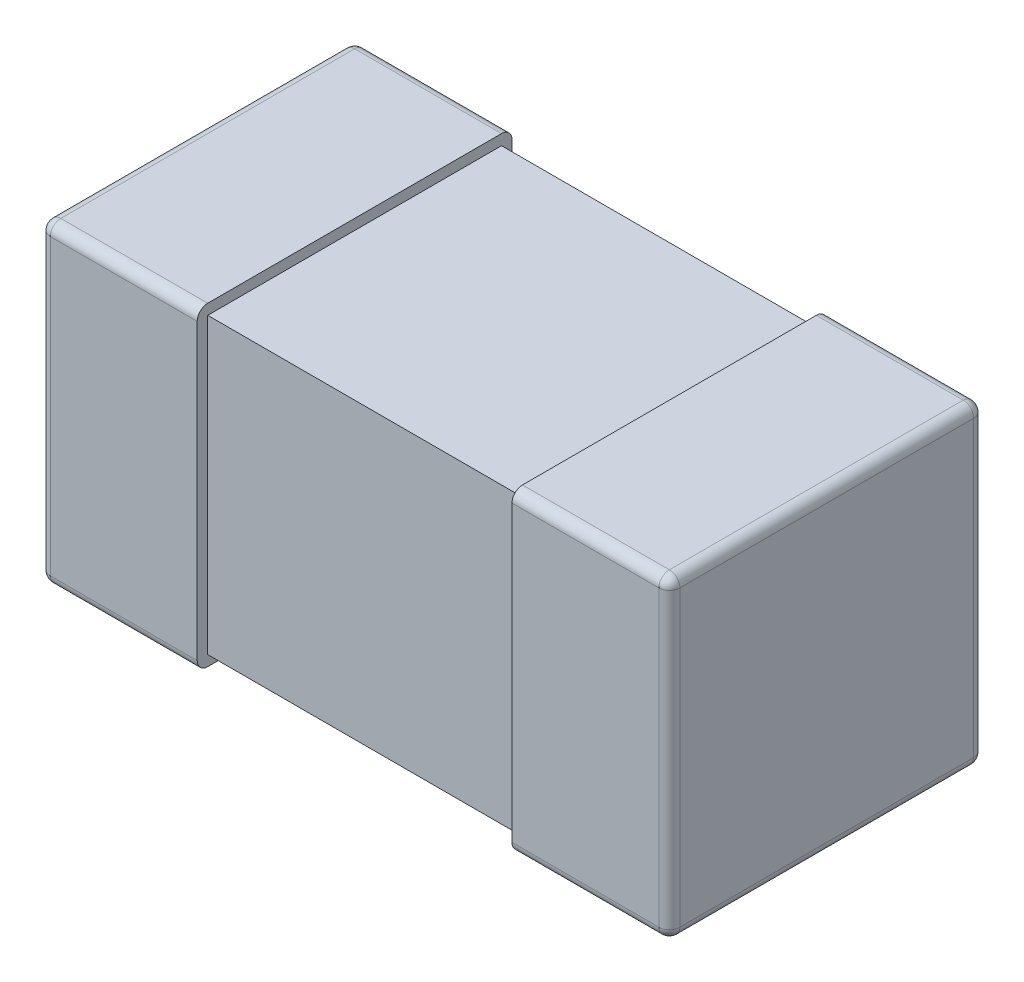
SolidWorks part; units mm, degrees
ref_plane "Front Plane" through (0, 0, 0) normal (0, 0, 1) x (1, 0, 0)
ref_plane "Top Plane" through (0, 0, 0) normal (0, 1, 0) x (1, 0, 0)
ref_plane "Right Plane" through (0, 0, 0) normal (1, 0, 0) x (0, 0, -1)
sketch "Sketch1" plane through (0, 0, 0) normal (0, 1, 0) x (1, 0, 0)
  line L0 (0, 0.15) -> (0, -0.15) construction
  line L1 (-0.3, 0) -> (0, 0) construction
  line L3 (-0.3, 0.15) -> (-0.15, 0.15)
  line L4 (-0.3, 0.15) -> (-0.3, -0.15)
  line L5 (-0.3, -0.15) -> (-0.15, -0.15)
  line L6 (-0.15, 0.15) -> (-0.15, -0.15)
  dimension "BANDWIDTH" = 0.15
  dimension "WIDTH" = 0.3
  dimension "LENGTH-HALF" = 0.3
extrude "THICKNESS" add sketch "Sketch1" along normal mid plane 0.3
fillet "Fillet1" radius 0.01 8 edges at (-0.3, -0.15, 0) (-0.225, -0.15, -0.15) (-0.3, 0, -0.15) (-0.225, -0.15, 0.15) (-0.3, 0, 0.15) (-0.3, 0.15, 0) (-0.225, 0.15, -0.15) (-0.225, 0.15, 0.15)
sketch "Sketch2" plane through (0, 0, 0) normal (1, 0, 0) x (0, 0, -1)
  line L0 (0, 0.15) -> (0, -0.15) construction
  line L1 (-0.14, 0.14) -> (0.14, 0.14)
  line L2 (-0.14, 0.14) -> (-0.14, -0.14)
  line L3 (-0.14, -0.14) -> (0.14, -0.14)
  line L4 (0.14, 0.14) -> (0.14, -0.14)
  line L5 (-0.14, 0.15) -> (0.14, 0.15) construction
  line L6 (-0.14, -0.15) -> (0.14, -0.15) construction
  line L7 (-0.15, 0) -> (0.15, 0) construction
  line L8 (-0.15, 0.14) -> (-0.15, -0.14) construction
  line L9 (0.15, 0.14) -> (0.15, -0.14) construction
  dimension "D1" = 0.01
  dimension "D2" = 0.01
extrude "Boss-Extrude2" add sketch "Sketch2" against normal up to surface (0.15 mm away) up to face at (-0.15, 0, 0)
mirror "Mirror3" about plane through (0, 0, 0) normal (1, 0, 0) of "Boss-Extrude2", "Fillet1", "THICKNESS"
